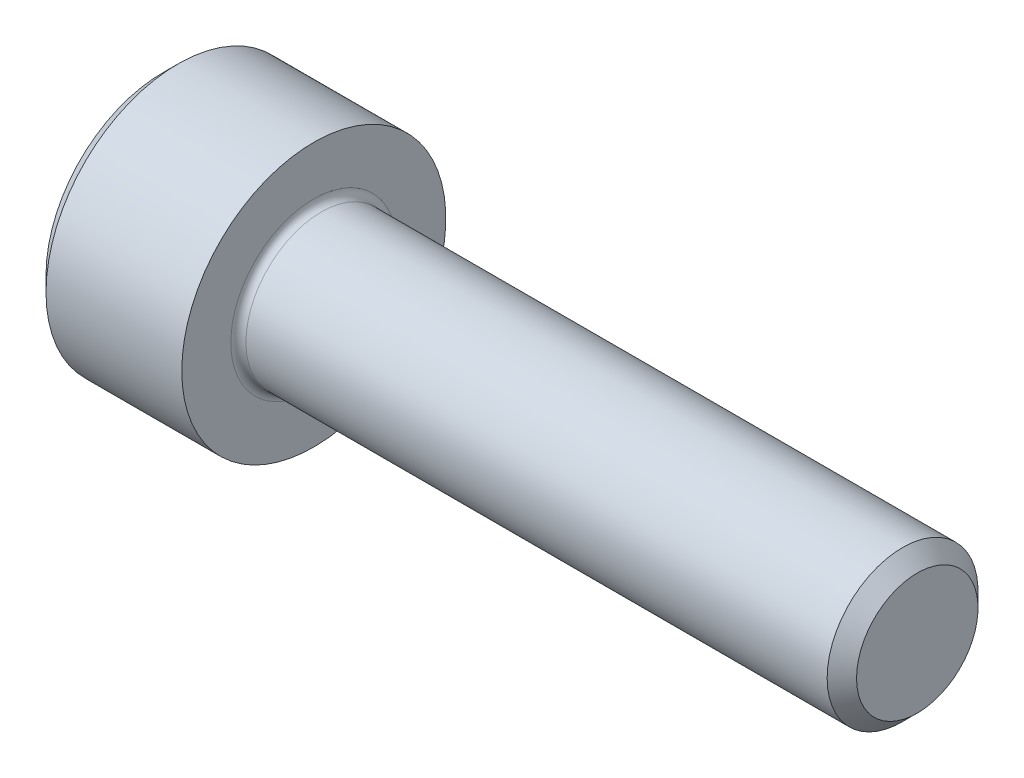
SolidWorks part; units mm, degrees
revolve "Base-Revolve" add sketch "BodySke"
sketch "BodySke" plane through (0, 0, 0) normal (0, 0, 1) x (1, 0, 0)
  line L0 (0, 0) -> (0, 3.1)
  line L1 (0.4, 3.5) -> (4, 3.5)
  line L2 (4, 3.5) -> (4, 2)
  line L3 (4, 2) -> (19.61, 2)
  line L4 (20, 1.61) -> (20, 0)
  line L5 (20, 0) -> (0, 0)
  line L6 (-31.75, 0) -> (127, 0) construction
  line L7 (0, 3.1) -> (0.4, 3.5)
  line L8 (20, 1.61) -> (19.61, 2)
  line L9 (0, -3.1) -> (0.4, -3.5) construction
  line L10 (20, -1.61) -> (19.61, -2) construction
  line L11 (4.7, 9.525) -> (4.7, 3.175) construction
  line L12 (4, 9.525) -> (4, 3.175) construction
  line L13 (-30, 9.525) -> (-30, 3.175) construction
  dimension "Diameter" = 4
  dimension "Head_ht" = 4
  dimension "Length" = 16
  dimension "Body_ch_ang" = 45
  dimension "Head_dia" = 7
  dimension "Head_ch_ang" = 45
  dimension "Minor_dia" = 3.22
  dimension "Advance" = 0.7
  dimension "Thread_nom" = 16
  dimension "Thread_length" = 50
  dimension "Head_ch_ht" = 0.4
cosmetic thread "ThreadCosmetic" [suppressed]
fillet "Fillet1" radius 0.2 1 edges at (4, 0, 2)
ref_plane "Plane1" through (0, 0, 0) normal (0, 0, 1) x (1, 0, 0)
ref_plane "Plane2" through (0, 0, 0) normal (0, 1, 0) x (1, 0, 0)
ref_plane "Plane3" through (0, 0, 0) normal (1, 0, 0) x (0, 0, -1)
sketch "Sketch2" plane through (0, 0, 0) normal (0, 0, 1) x (1, 0, 0)
  line L0 (0, 1.5355) -> (2, 1.5355)
  line L1 (2, 1.5355) -> (2.8865, 0)
  line L2 (-31.75, 0) -> (127, 0) construction
  line L3 (2.8865, 0) -> (0, 0)
  line L4 (0, 0) -> (0, 1.5355)
  line L5 (0, 3.1) -> (0, -3.1) construction
  line L6 (0, 0) -> (47.625, 0) construction
  line L7 (4, -3.5) -> (4, 3.5) construction
  dimension "D1" = 1.5355
  dimension "D2" = 60
revolve "Hex-PreBroach" cut sketch "Sketch2" angle 360 about L6
sketch "Sketch3" plane through (0, 0, 0) normal (-1, 0, 0) x (0, 0.5, 0.866)
  line L0 (0.8865, 1.5355) -> (-0.8865, 1.5355)
  line L1 (-0.8865, 1.5355) -> (-1.773, 0)
  line L2 (0.8865, 1.5355) -> (1.773, 0)
  line L3 (0.8865, -1.5355) -> (1.773, 0)
  line L4 (0.8865, -1.5355) -> (-0.8865, -1.5355)
  line L5 (-0.8865, -1.5355) -> (-1.773, 0)
  dimension "D1" = 1.5355
  dimension "D2" = 1.5355
  dimension "Hex_size" = 3.071
extrude "Hex" cut sketch "Sketch3" against normal blind 2
sketch "Sketch4" plane through (0, 0, 0) normal (-1, 0, 0) x (0, 0, 1)
  line L0 (0, 0) -> (1.7399, 0)
  line L1 (0, 0) -> (6.1484, 3.5498) construction
  line L2 (0, 0) -> (0.8699, 1.5068)
  line L3 (1.4457, 0.3947) -> (1.6607, 0.5189)
  line L4 (1.0647, 1.0546) -> (1.2797, 1.1788)
  arc A0 (1.4457, 0.3947) -> (1.0647, 1.0546) centre (0, 0) ccw
  arc A1 (1.7399, 0) -> (1.6607, 0.5189) centre (0, 0) ccw
  arc A2 (0.8699, 1.5068) -> (1.2797, 1.1788) centre (0, 0) cw
  dimension "D1" = 30
  dimension "D2" = 60
  dimension "Spline_p_dim" = 0.762
  dimension "D3" = 0.381
extrude "Spline" [suppressed] cut sketch "Sketch4" against normal blind 2
pattern_circular "CirPattern1" [suppressed] count 6 every 60
sketch "Sketch5" plane through (0, 0, 0) normal (0, 0, 1) x (1, 0, 0)
  line L0 (-31.75, 0) -> (127, 0) construction
  line L2 (0, 3.1) -> (0, -3.1) construction
  circle A0 centre (1.6, 0) radius 0.675
  dimension "Drilled_hole_dia" = 1.35
  dimension "Drilled_hole_loc" = 1.6
extrude "Hole" [suppressed] cut sketch "Sketch5" against normal through all and the other way through all
pattern_circular "Drilled-4" [suppressed] count 2 every 60
pattern_circular "Drilled-6" [suppressed] count 3 every 60
sketch "ThdSchSke" plane through (0, 0, 0) normal (0, 0, 1) x (1, 0, 0)
  line L0 (4.7, -1.61) -> (4.4269, -2)
  line L1 (4.7, -1.61) -> (4.9731, -2)
  line L2 (4.9731, -2) -> (4.9731, -2.5)
  line L3 (-3.175, 0) -> (5.1513, 0) construction
  line L5 (4.9731, -2.5) -> (4.4269, -2.5)
  line L6 (4.4269, -2.5) -> (4.4269, -2)
  line L7 (0, 3.1) -> (0, -3.1) construction
  dimension "Thread_minor" = 3.22
  dimension "Diameter" = 4
  dimension "Start" = 4.7
revolve "ThreadSchematic" [suppressed] cut sketch "ThdSchSke" angle 360 about L3
pattern_linear "ThdSchPat" [suppressed]
equation "\"D2@Sketch3\" = \"Hex_size@Sketch3\" / 2"
equation "\"D1@Sketch3\" = \"Hex_size@Sketch3\" / 2"
equation "\"D1@Sketch2\" = \"Hex_size@Sketch3\" / 2"
equation "\"D3@Sketch4\" = \"Spline_p_dim@Sketch4\" / 2"
equation "\"Thread_minor@ThreadCosmetic\"  =  \"Minor_dia@BodySke\""
equation "\"D2@CirPattern1\" = 360 / \"Num_teeth@CirPattern1\""
equation "\"Wall_thickness@Sketch2\" = \"Head_ht@BodySke\" - \"Key_eng@Hex\""
equation "\"Thread_length@ThreadCosmetic\" = ((sgn( (\"Length@BodySke\" - \"Advance@BodySke\" ) - \"Thread_nom@BodySke\" )-1)*( (\"Length@BodySke\" - \"Advance@BodySke\" ) - \"Thread_nom@BodySke\" ))/-2+ \"Thread_nom@BodySke\""
equation "\"Thread_minor@ThdSchSke\" = \"Minor_dia@BodySke\""
equation "\"Diameter@ThdSchSke\" = \"Diameter@BodySke\""
equation "\"Overcut@ThdSchSke\" = \"Diameter@BodySke\" * 1.25"
equation "\"Start@ThdSchSke\" = \"Head_ht@BodySke\" + \"Length@BodySke\" - \"Thread_length@ThreadCosmetic\"  '---Non-countersunk---"
equation "\"Num_threads@ThdSchPat\" = int( \"Thread_length@ThreadCosmetic\" / \"Advance@BodySke\" + 0.999 )  + 1"
equation "\"Advance@ThdSchPat\" = \"Thread_length@ThreadCosmetic\" /  (\"Num_threads@ThdSchPat\" - 1) 'relax it"
equation "\"Num_threads@ThdSchPat\" = \"Num_threads@ThdSchPat\" - sgn( \"Num_threads@ThdSchPat\" - 1) '---chamfered tips only---"
